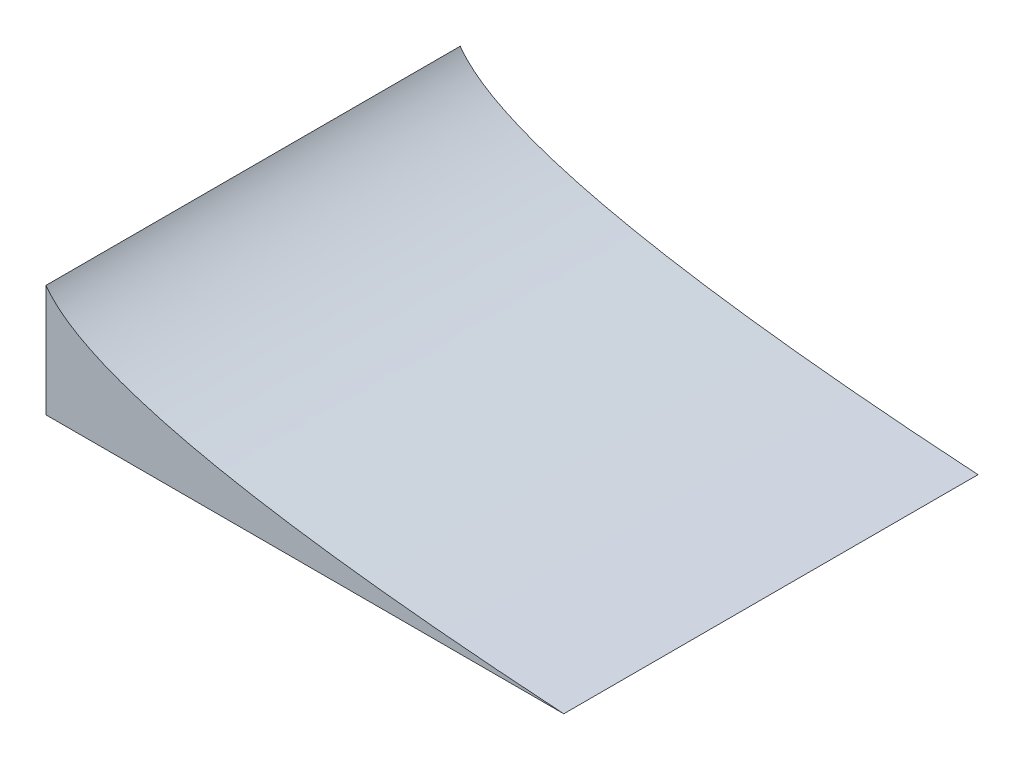
SolidWorks part; units mm, degrees
ref_plane "Front Plane" through (0, 0, 0) normal (0, 0, 1) x (1, 0, 0)
ref_plane "Top Plane" through (0, 0, 0) normal (0, 1, 0) x (1, 0, 0)
ref_plane "Right Plane" through (0, 0, 0) normal (1, 0, 0) x (0, 0, -1)
sketch "Sketch1" plane through (0, 0, 0) normal (0, 0, 1) x (1, 0, 0)
  line L0 (-381, 0) -> (381, 0)
  line L1 (-381, 0) -> (-381, 165.1)
  line L2 (-381, 165.1) -> (-296.0032, 43.712) construction
  line L3 (-296.0032, 43.712) -> (381, 0) construction
  spline S0 degree 2 poles (-381, 165.1) (-296.0032, 43.712) (381, 0) knots 0 0 0 1 1 1
  point P5 (0, 0)
  point P8 (-269.0772, 81.3728)
  point P9 (-221.2177, 86.3289)
  point P10 (-252.8203, 13.8743)
  point P11 (-240.4876, 57.8095)
  point P12 (-322.8465, 28.8001)
  dimension "D1" = 762
  dimension "D2" = 165.1
  dimension "D3" = 35
extrude "Boss-Extrude1" add sketch "Sketch1" against normal blind 609.6
